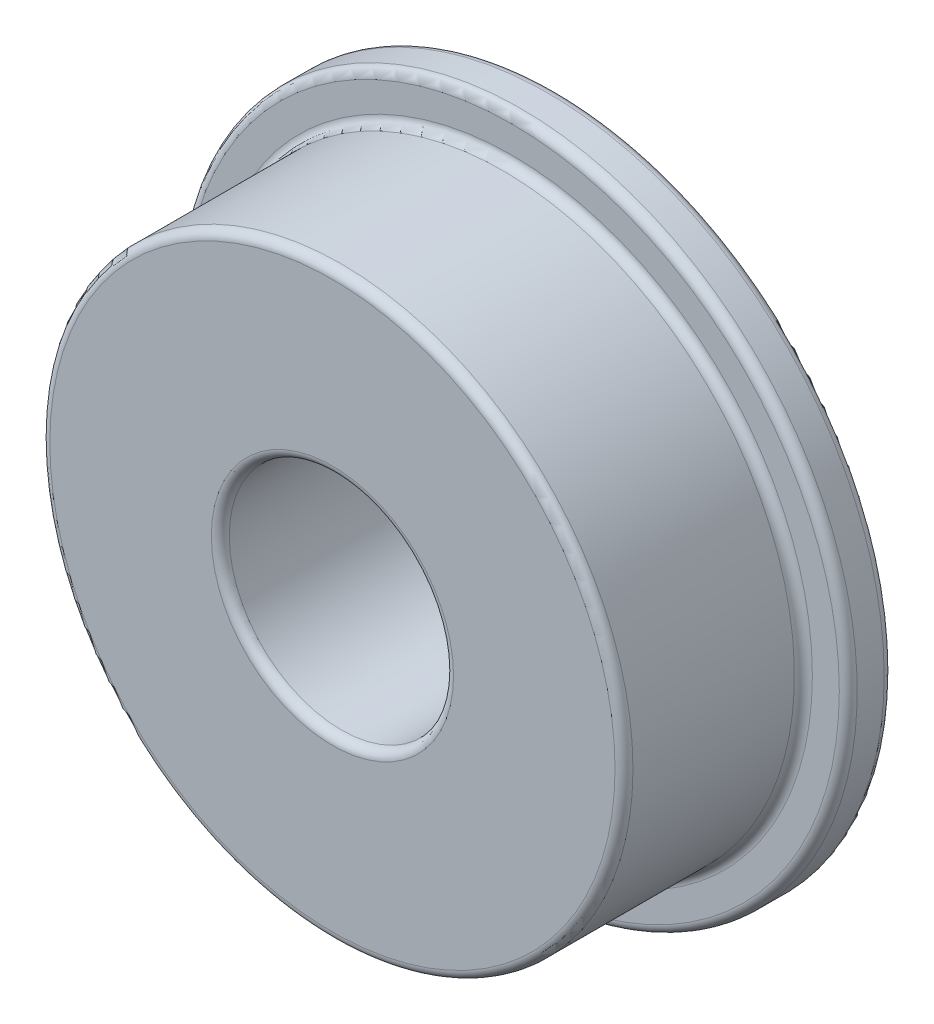
SolidWorks part; units mm, degrees
ref_plane "前视基准面" through (0, 0, 0) normal (0, 0, 1) x (1, 0, 0)
ref_plane "上视基准面" through (0, 0, 0) normal (0, 1, 0) x (1, 0, 0)
ref_plane "右视基准面" through (0, 0, 0) normal (1, 0, 0) x (0, 0, -1)
sketch "草图1" plane through (0, 0, 0) normal (0, 0, 1) x (1, 0, 0)
  circle A0 centre (0, 0) radius 2.5
  circle A1 centre (0, 0) radius 6.5
  dimension "D1" = 5
  dimension "D2" = 13
extrude "凸台-拉伸1" add sketch "草图1" along normal blind 5
sketch "草图2" plane through (0, 0, 0) normal (0, 0, -1) x (-1, 0, 0)
  circle A0 centre (0, 0) radius 2.5
  circle A1 centre (0, 0) radius 7.5
  dimension "D1" = 15
extrude "凸台-拉伸2" add sketch "草图2" against normal blind 1
fillet "圆角1" radius 0.2 6 edges at (-6.5, 0, 1) (6.5, 0, 5) (2.5, 0, 5) (2.5, 0, 0) (-7.5, 0, 1) (-7.5, 0, 0)
